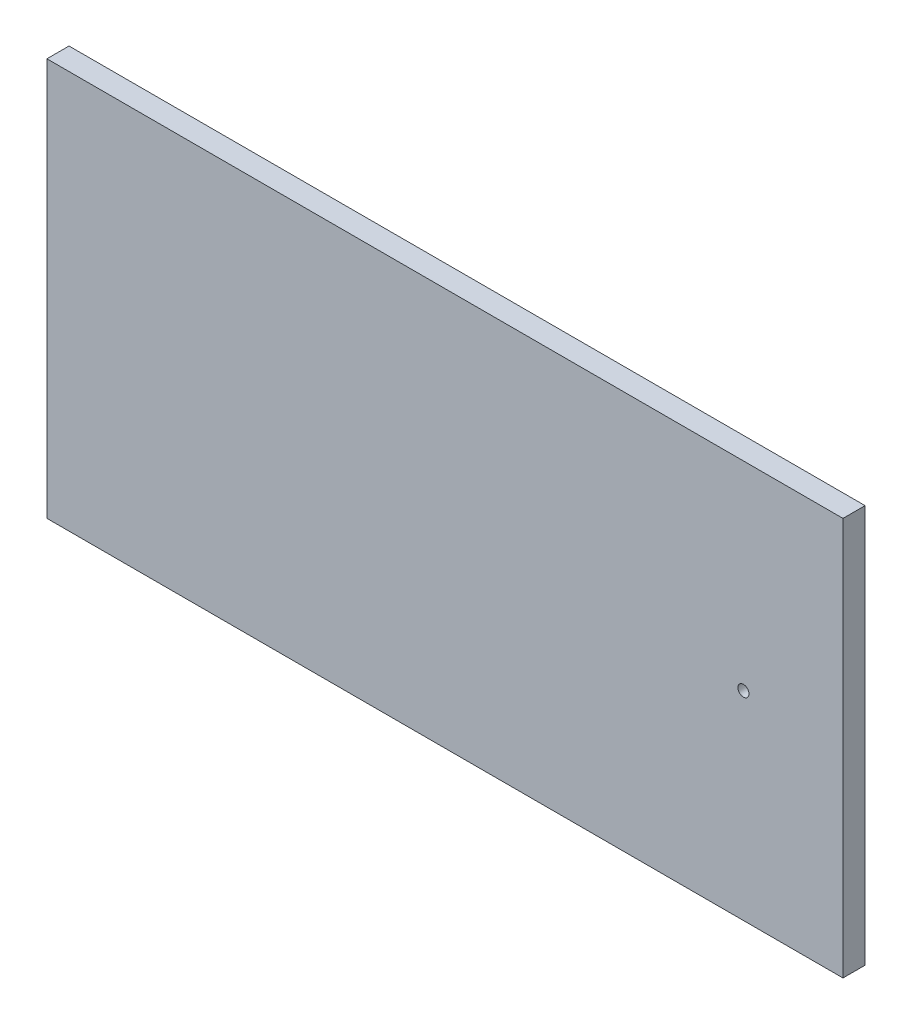
SolidWorks part; units mm, degrees
ref_plane "Front Plane" through (0, 0, 0) normal (0, 0, 1) x (1, 0, 0)
ref_plane "Top Plane" through (0, 0, 0) normal (0, 1, 0) x (1, 0, 0)
ref_plane "Right Plane" through (0, 0, 0) normal (1, 0, 0) x (0, 0, -1)
sketch "Sketch2" plane through (0, 0, 0) normal (0, 0, 1) x (1, 0, 0)
  line L1 (0, 0) -> (457.2, 0)
  line L2 (0, 0) -> (0, -228.6)
  line L3 (0, -228.6) -> (457.2, -228.6)
  line L4 (457.2, 0) -> (457.2, -228.6)
  dimension "D1" = 457.2
  dimension "D2" = 228.6
extrude "Boss-Extrude1" add sketch "Sketch2" along normal blind 12.7
sketch "Sketch3" plane through (0, 0, 12.7) normal (0, 0, 1) x (1, 0, 0)
  line L1 (457.2, -228.6) -> (457.2, 0) construction
  circle A1 centre (400.05, -114.3) radius 3.175
  dimension "D4" = 6.35
  dimension "D3" = 57.15
extrude "Cut-Extrude1" cut sketch "Sketch3" against normal blind 12.7
